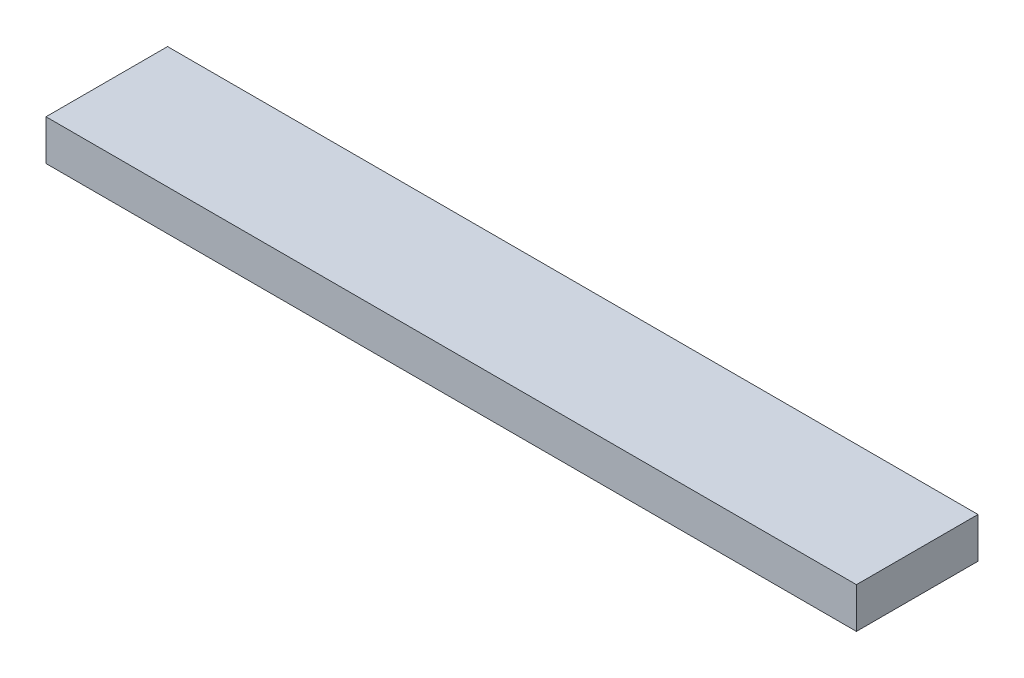
SolidWorks part; units mm, degrees
ref_plane "Front Plane" through (0, 0, 0) normal (0, 0, 1) x (1, 0, 0)
ref_plane "Top Plane" through (0, 0, 0) normal (0, 1, 0) x (1, 0, 0)
ref_plane "Right Plane" through (0, 0, 0) normal (1, 0, 0) x (0, 0, -1)
sketch "Sketch1" plane through (0, 0, 0) normal (0, 1, 0) x (1, 0, 0)
  line L1 (0, 0) -> (200, 0)
  line L2 (0, 0) -> (0, 30)
  line L3 (0, 30) -> (200, 30)
  line L4 (200, 0) -> (200, 30)
  dimension "D1" = 30
  dimension "D2" = 200
extrude "Boss-Extrude1" add sketch "Sketch1" along normal blind 10
